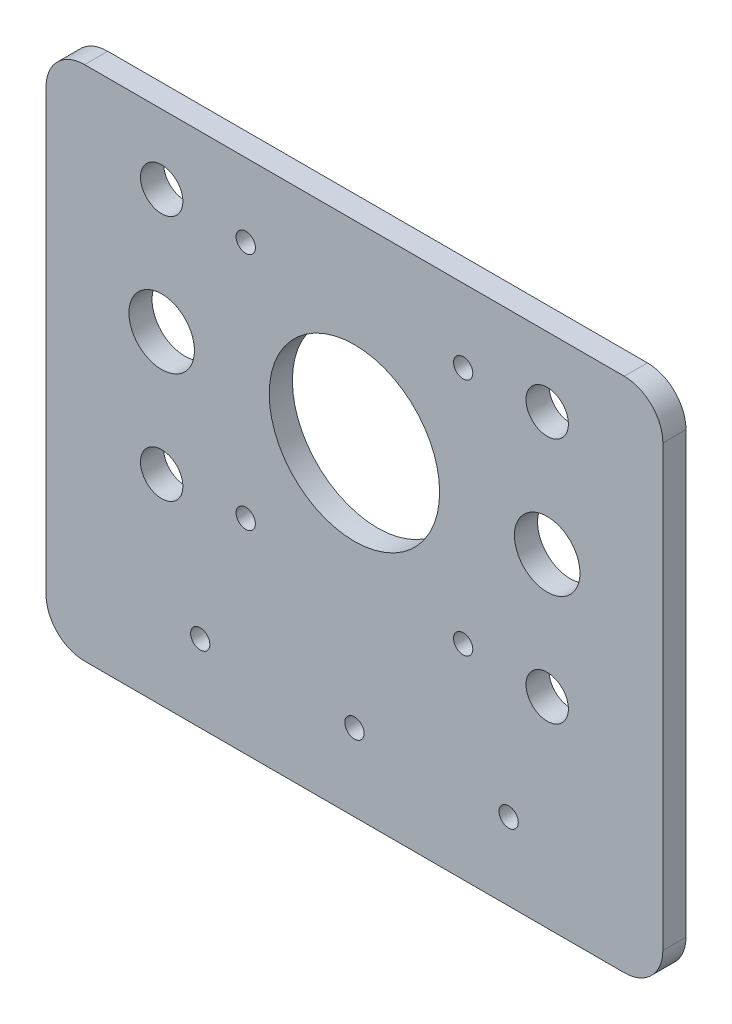
SolidWorks part; units mm, degrees
ref_plane "前视基准面" through (0, 0, 0) normal (0, 0, 1) x (1, 0, 0)
ref_plane "上视基准面" through (0, 0, 0) normal (0, 1, 0) x (1, 0, 0)
ref_plane "右视基准面" through (0, 0, 0) normal (1, 0, 0) x (0, 0, -1)
sketch "草图1" plane through (0, 0, 0) normal (0, 0, 1) x (1, 0, 0)
  line L0 (-73.587, 0) -> (88.4753, 0) construction
  line L1 (0, 53.9394) -> (0, -52.9631) construction
  line L2 (-73.587, -15.5) -> (88.4753, -15.5) construction
  line L3 (-15.5, 53.9394) -> (-15.5, -52.9631) construction
  line L4 (-73.587, 15.5) -> (88.4753, 15.5) construction
  line L5 (15.5, 53.9394) -> (15.5, -52.9631) construction
  line L6 (-25, 53.9394) -> (-25, -52.9631) construction
  line L7 (25, 53.9394) -> (25, -52.9631) construction
  line L8 (-73.587, -16) -> (88.4753, -16) construction
  line L9 (-73.587, 16) -> (88.4753, 16) construction
  line L10 (-73.587, -32) -> (88.4753, -32) construction
  line L11 (-20, 53.9394) -> (-20, -52.9631) construction
  line L12 (20, 53.9394) -> (20, -52.9631) construction
  line L13 (-40, 20) -> (-40, -37)
  line L14 (40, 20) -> (40, -37)
  line L15 (-35, -42) -> (35, -42)
  line L16 (-35, 25) -> (35, 25)
  line L17 (-40, 53.9394) -> (-40, -52.9631) construction
  line L18 (-73.587, -42) -> (88.4753, -42) construction
  line L19 (40, 53.9394) -> (40, -52.9631) construction
  line L20 (-73.587, 25) -> (88.4753, 25) construction
  circle A0 centre (0, 0) radius 11.05
  circle A5 centre (-25, 16) radius 2.75
  circle A6 centre (-25, -16) radius 2.75
  circle A7 centre (25, -16) radius 2.75
  circle A8 centre (25, 16) radius 2.75
  circle A9 centre (0, -32) radius 1.25
  circle A10 centre (-20, -32) radius 1.25
  circle A11 centre (20, -32) radius 1.25
  circle A12 centre (-25, 0) radius 4.25
  circle A13 centre (25, 0) radius 4.25
  arc A14 (-40, -37) -> (-35, -42) centre (-35, -37) ccw
  arc A15 (35, -42) -> (40, -37) centre (35, -37) ccw
  arc A16 (40, 20) -> (35, 25) centre (35, 20) ccw
  arc A17 (-35, 25) -> (-40, 20) centre (-35, 20) ccw
  circle A18 centre (-14.1, 15.5) radius 1.25
  circle A19 centre (14.1, 15.5) radius 1.25
  circle A20 centre (14.1, -15.5) radius 1.25
  circle A21 centre (-14.1, -15.5) radius 1.25
  dimension "D1" = 22.1
  dimension "D4" = 2.5
  dimension "D10" = 5.5
  dimension "D11" = 5.5
  dimension "D15" = 2.5
  dimension "D16" = 8.5
  dimension "D21" = 5
  dimension "D5" = 2.5
  dimension "D2" = 15.5
  dimension "D22" = 28.2
  dimension "D23" = 14.1
  dimension "D3" = 15.5
  dimension "D6" = 25
  dimension "D7" = 25
  dimension "D8" = 16
  dimension "D9" = 16
  dimension "D12" = 32
  dimension "D13" = 20
  dimension "D14" = 20
  dimension "D17" = 40
  dimension "D18" = 40
  dimension "D19" = 10
  dimension "D20" = 67
extrude "凸台-拉伸1" add sketch "草图1" along normal blind 3
